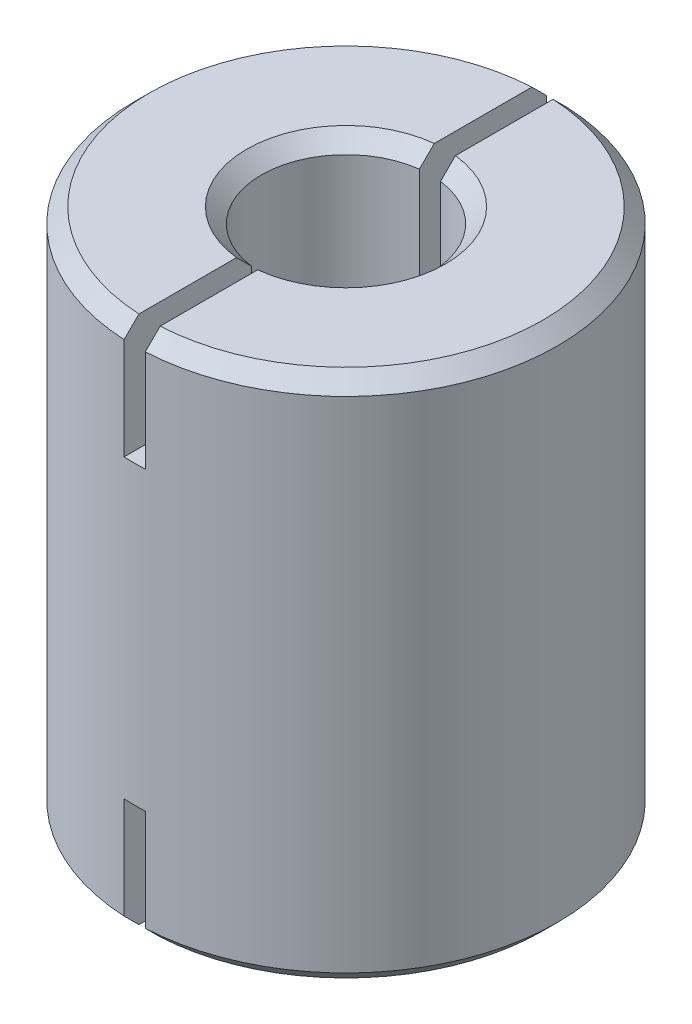
SolidWorks part; units mm, degrees
ref_plane "Front Plane" through (0, 0, 0) normal (0, 0, 1) x (1, 0, 0)
ref_plane "Top Plane" through (0, 0, 0) normal (0, 1, 0) x (1, 0, 0)
ref_plane "Right Plane" through (0, 0, 0) normal (1, 0, 0) x (0, 0, -1)
sketch "Sketch1" plane through (0, 0, 0) normal (0, 1, 0) x (1, 0, 0)
  circle A0 centre (0, 0) radius 4
  circle A1 centre (0, 0) radius 10
  dimension "D1" = 20
  dimension "D2" = 8
extrude "Boss-Extrude1" add sketch "Sketch1" along normal mid plane 25
chamfer "Chamfer1" distance 0.7 angle 45 4 edges at (0, -12.5, 4) (0, -12.5, 10) (0, 12.5, 4) (0, 12.5, 10)
sketch "Sketch2" plane through (0, 0, 0) normal (0, 0, 1) x (1, 0, 0)
  line L0 (0, 0) -> (13.1702, 0) construction
  line L1 (0.5, 27.3629) -> (-0.5, 27.3629)
  line L2 (0.5, 27.3629) -> (0.5, 7)
  line L3 (0.5, 7) -> (-0.5, 7)
  line L4 (-0.5, 27.3629) -> (-0.5, 7)
  line L5 (0.5, 27.3629) -> (-0.5, 7) construction
  line L6 (0.5, 7) -> (-0.5, 27.3629) construction
  line L7 (0.5, -7) -> (-0.5, -27.3629) construction
  line L8 (0.5, -27.3629) -> (-0.5, -7) construction
  line L9 (-0.5, -27.3629) -> (-0.5, -7)
  line L10 (0.5, -7) -> (-0.5, -7)
  line L11 (0.5, -27.3629) -> (0.5, -7)
  line L12 (0.5, -27.3629) -> (-0.5, -27.3629)
  point P0 (0, 17.1814)
  point P12 (0, -17.1814)
  dimension "D1" = 1
  dimension "D2" = 14
extrude "Cut-Extrude1" cut sketch "Sketch2" against normal blind 36 and the other way blind 40
